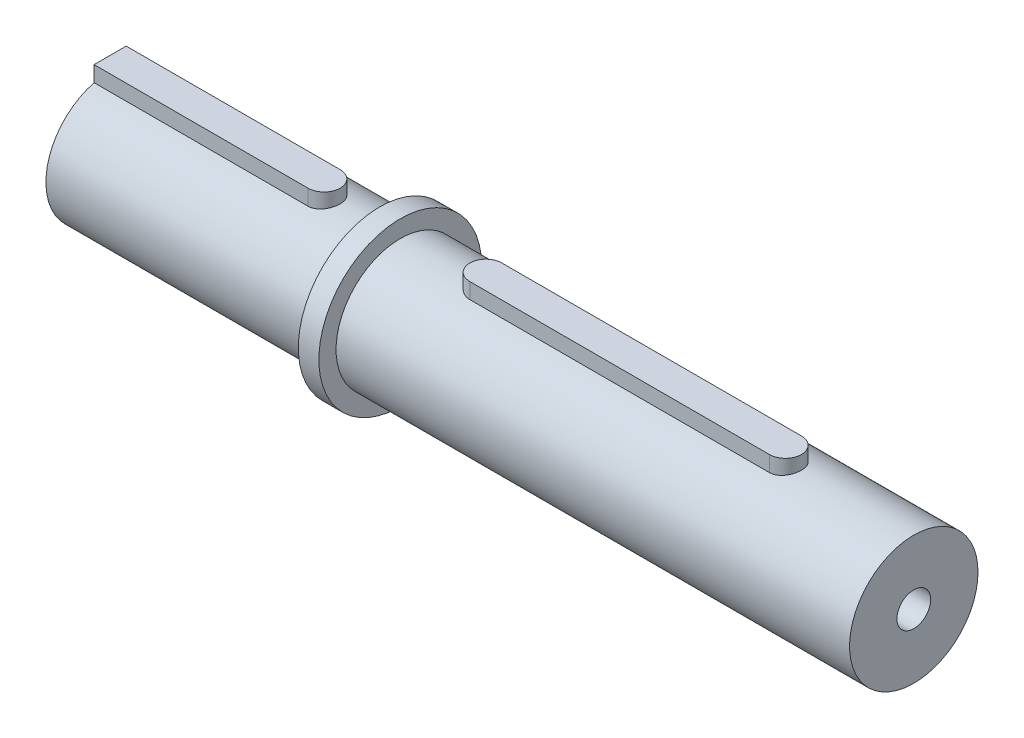
SolidWorks part; units mm, degrees
ref_plane "Front Plane" through (0, 0, 0) normal (0, 0, 1) x (1, 0, 0)
ref_plane "Top Plane" through (0, 0, 0) normal (0, 1, 0) x (1, 0, 0)
ref_plane "Right Plane" through (0, 0, 0) normal (1, 0, 0) x (0, 0, -1)
sketch "Sketch1" plane through (0, 0, 0) normal (1, 0, 0) x (0, 0, -1)
  circle A0 centre (0, 0) radius 12.0777
  dimension "D1" = 24.1554
extrude "Boss-Extrude1" add sketch "Sketch1" against normal blind 3.048
sketch "Sketch2" plane through (-3.048, 0, 0) normal (-1, 0, 0) x (0, 0, 1)
  circle A0 centre (0, 0) radius 9.525
  dimension "D1" = 19.05
extrude "Boss-Extrude2" add sketch "Sketch2" along normal blind 40
sketch "Sketch3" plane through (0, 0, 0) normal (1, 0, 0) x (0, 0, -1)
  circle A0 centre (0, 0) radius 9.525
  dimension "D1" = 19.05
extrude "Boss-Extrude3" add sketch "Sketch3" along normal blind 76.2
hole_wizard "M6 Tapped Hole1" positions "Sketch5" profile "Sketch4" tap size "M6" standard "DIN"
sketch "Sketch5" plane through (76.2, 0, 0) normal (1, 0, 0) x (0, 0, -1)
  point P0 (0, 0)
sketch "Sketch4" plane through (76.2, 0, 0) normal (0, 1, 0) x (0, 0, -1)
  line L0 (0, 0) -> (0, 16.4882)
  line L1 (0, 16.4882) -> (2.5, 14.986)
  line L2 (2.5, 14.986) -> (2.5, 0)
  line L5 (2.5, 0) -> (0, 0)
  line L10 (0, 16.4882) -> (-2.5, 14.986) construction
  line L11 (0, -6.35) -> (0, 107.95) construction
  dimension "Tap Drill Dia." = 5
  dimension "Tap Drill Depth" = 14.986
  dimension "Drill Angle" = 118
cosmetic thread "Hole Thread1" parameters "D1"=9.906, "D2"=6
ref_plane "Plane2" through (0, 6.7818, 0) normal (0, 1, 0) x (1, 0, 0)
sketch "Sketch33" plane through (0, 6.7818, 0) normal (0, 1, 0) x (1, 0, 0)
  line L0 (12.7, 0) -> (57.15, 0) construction
  line L1 (12.7, 2.3813) -> (57.15, 2.3813)
  line L2 (12.7, -2.3813) -> (57.15, -2.3813)
  line L3 (76.2, -9.525) -> (76.2, 9.525) construction
  line L4 (-43.048, 0) -> (-11.298, 0) construction
  line L5 (-43.048, 9.525) -> (-43.048, -9.525) construction
  line L6 (-43.048, 2.3813) -> (-11.298, 2.3813)
  line L7 (-43.048, -2.3813) -> (-11.298, -2.3813)
  line L8 (-43.048, 2.3813) -> (-43.048, -2.3813)
  arc A0 (12.7, 2.3813) -> (12.7, -2.3813) centre (12.7, 0) ccw
  arc A1 (57.15, -2.3813) -> (57.15, 2.3813) centre (57.15, 0) ccw
  arc A3 (-11.298, -2.3813) -> (-11.298, 2.3813) centre (-11.298, 0) ccw
  point P3 (34.925, 0)
  point P14 (-27.173, 0)
  dimension "D1" = 44.45
  dimension "D2" = 19.05
  dimension "D3" = 4.7625
  dimension "D4" = 4.7625
  dimension "D5" = 31.75
extrude "Boss-Extrude4" add sketch "Sketch33" along normal blind 4.7625
